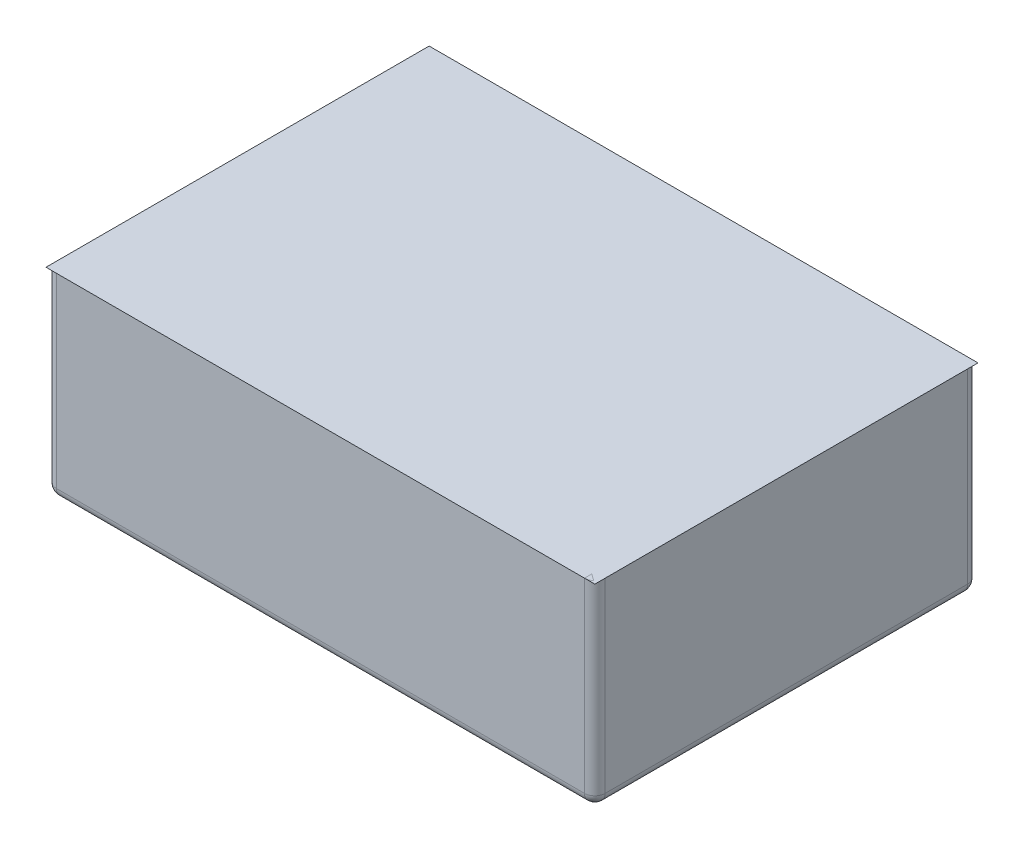
SolidWorks part; units mm, degrees
material "PVC Rigid"
ref_plane "Front Plane" through (0, 0, 0) normal (0, 0, 1) x (1, 0, 0)
ref_plane "Top Plane" through (0, 0, 0) normal (0, 1, 0) x (1, 0, 0)
ref_plane "Right Plane" through (0, 0, 0) normal (1, 0, 0) x (0, 0, -1)
sketch "Sketch1" plane through (0, 0, 0) normal (0, 1, 0) x (1, 0, 0)
  line L1 (-132.5, -92.5) -> (132.5, -92.5)
  line L2 (-132.5, -92.5) -> (-132.5, 92.5)
  line L3 (-132.5, 92.5) -> (132.5, 92.5)
  line L4 (132.5, -92.5) -> (132.5, 92.5)
  line L5 (-132.5, -92.5) -> (132.5, 92.5) construction
  line L6 (-132.5, 92.5) -> (132.5, -92.5) construction
  point P0 (0, 0)
  dimension "D1" = 265
  dimension "D2" = 185
extrude "Boss-Extrude1" add sketch "Sketch1" along normal blind 95
sketch "Sketch2" plane through (0, 95, 0) normal (0, 1, 0) x (1, 0, 0)
  line L1 (-127.5, -87.5) -> (127.5, -87.5)
  line L2 (-127.5, -87.5) -> (-127.5, 87.5)
  line L3 (-127.5, 87.5) -> (127.5, 87.5)
  line L4 (127.5, -87.5) -> (127.5, 87.5)
  line L5 (-127.5, -87.5) -> (127.5, 87.5) construction
  line L6 (-127.5, 87.5) -> (127.5, -87.5) construction
  point P0 (0, 0)
  dimension "D1" = 255
  dimension "D2" = 175
extrude "Cut-Extrude1" cut sketch "Sketch2" against normal blind 85
sketch "Sketch5" plane through (0, 95, 0) normal (0, 1, 0) x (1, 0, 0)
  line L4 (132.5, -92.5) -> (132.5, 92.5)
  line L5 (132.5, 92.5) -> (-132.5, 92.5)
  line L6 (-132.5, 92.5) -> (-132.5, -92.5)
  line L7 (-132.5, -92.5) -> (132.5, -92.5)
  line L8 (132.5, -92.5) -> (132.5, 92.5)
  line L9 (132.5, 92.5) -> (-132.5, 92.5)
  line L10 (-132.5, 92.5) -> (-132.5, -92.5)
  line L11 (-132.5, -92.5) -> (132.5, -92.5)
  dimension "D1" = 0
surface "Surface-Plane1" sketch "Sketch5"
sketch "Sketch6" plane through (0, 0, 0) normal (0, -1, 0) x (1, 0, 0)
  line L0 (0, -92.5) -> (0, 92.5) construction
  line L1 (-132.5, 92.5) -> (132.5, 92.5) construction
  line L2 (-132.5, 0) -> (132.5, 0) construction
  line L3 (-132.5, -92.5) -> (-132.5, 92.5) construction
  line L4 (132.5, 92.5) -> (132.5, -92.5) construction
  line L5 (-132.5, 55) -> (132.5, 55) construction
  line L6 (-132.5, -55) -> (132.5, -55) construction
  circle A0 centre (0, 55) radius 8.89
  circle A1 centre (0, -55) radius 8.89
  point P6 (0, 0)
  dimension "D3" = 17.78
  dimension "D4" = 17.78
  dimension "D1" = 55
  dimension "D2" = 55
extrude "Cut-Extrude2" cut sketch "Sketch6" against normal up to next
fillet "Fillet1" radius 5 8 edges at (0, 0, -92.5) (132.5, 0, 0) (0, 0, 92.5) (-132.5, 47.5, 92.5) (-132.5, 0, 0) (-132.5, 47.5, -92.5) (132.5, 47.5, 92.5) (132.5, 47.5, -92.5)
